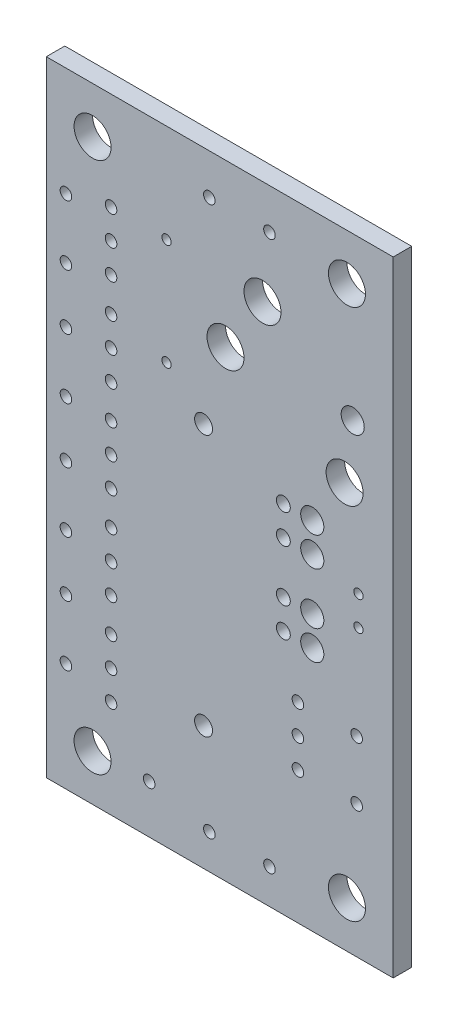
SolidWorks part; units mm, degrees
ref_plane "Plan de face" through (0, 0, 0) normal (0, 0, 1) x (1, 0, 0)
ref_plane "Plan de dessus" through (0, 0, 0) normal (0, 1, 0) x (1, 0, 0)
ref_plane "Plan de droite" through (0, 0, 0) normal (1, 0, 0) x (0, 0, -1)
sketch "Model" plane through (0, 0, 0) normal (0, 0, 1) x (1, 0, 0)
  line L1 (0, 0) -> (30, 0)
  line L2 (0, 0) -> (0, 54)
  line L3 (0, 54) -> (30, 54)
  line L4 (30, 0) -> (30, 54)
  circle A0 centre (1.7, 39.4) radius 0.5
  circle A1 centre (1.7, 44.6) radius 0.5
  circle A2 centre (1.7, 29.4) radius 0.5
  circle A3 centre (1.7, 34.6) radius 0.5
  circle A4 centre (1.7, 19.4) radius 0.5
  circle A5 centre (1.7, 24.6) radius 0.5
  circle A6 centre (1.7, 9.4) radius 0.5
  circle A7 centre (1.7, 14.6) radius 0.5
  circle A8 centre (14.1, 50.5) radius 0.5
  circle A9 centre (19.3, 50.5) radius 0.5
  circle A10 centre (19.3, 3) radius 0.5
  circle A11 centre (14.1, 3) radius 0.5
  circle A12 centre (5.6, 45.54) radius 0.5
  circle A13 centre (5.6, 43) radius 0.5
  circle A14 centre (5.6, 40.46) radius 0.5
  circle A15 centre (5.6, 37.5217) radius 0.5
  circle A16 centre (5.6, 34.9817) radius 0.5
  circle A17 centre (5.6, 32.4417) radius 0.5
  circle A18 centre (5.6, 29.54) radius 0.5
  circle A19 centre (5.6, 27) radius 0.5
  circle A20 centre (5.6, 24.46) radius 0.5
  circle A21 centre (5.6, 21.54) radius 0.5
  circle A22 centre (5.6, 19) radius 0.5
  circle A23 centre (5.6, 16.46) radius 0.5
  circle A24 centre (5.6, 13.54) radius 0.5
  circle A25 centre (5.6, 11) radius 0.5
  circle A26 centre (5.6, 8.46) radius 0.5
  circle A27 centre (15.498, 39.999) radius 1.6
  circle A28 centre (18.698, 45) radius 1.6
  circle A29 centre (25.798, 35) radius 1.6
  circle A30 centre (26.4983, 39.9992) radius 1
  circle A31 centre (20.5, 28.23) radius 0.6
  circle A32 centre (20.5, 30.77) radius 0.6
  circle A33 centre (23, 30.77) radius 1
  circle A34 centre (23, 28.23) radius 1
  circle A35 centre (20.5, 21.23) radius 0.6
  circle A36 centre (20.5, 23.77) radius 0.6
  circle A37 centre (23, 23.77) radius 1
  circle A38 centre (23, 21.23) radius 1
  circle A39 centre (13.6, 33.3) radius 0.775
  circle A40 centre (13.6, 10.7) radius 0.775
  circle A41 centre (26, 4) radius 1.6
  circle A42 centre (4, 4) radius 1.6
  circle A43 centre (26, 50) radius 1.6
  circle A44 centre (4, 50) radius 1.6
  circle A45 centre (26.9977, 27.2723) radius 0.4
  circle A46 centre (26.9977, 24.7323) radius 0.4
  circle A47 centre (10.4, 45.5) radius 0.4
  circle A48 centre (10.4, 36.3) radius 0.4
  circle A49 centre (21.7605, 14) radius 0.5
  circle A50 centre (21.7605, 11.46) radius 0.5
  circle A51 centre (26.8405, 11.46) radius 0.5
  circle A52 centre (26.8405, 16.54) radius 0.5
  circle A53 centre (21.7605, 16.54) radius 0.5
  circle A54 centre (8.8994, 4.172) radius 0.5
extrude "Boss.-Extru.1" add sketch "Model" along normal blind 1.6
